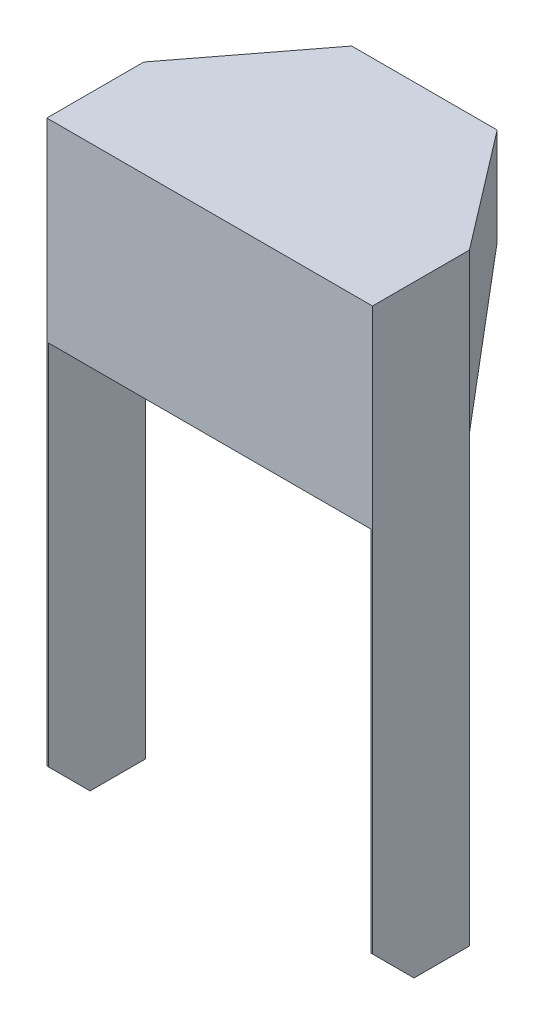
SolidWorks part; units mm, degrees
ref_plane "Front Plane" through (0, 0, 0) normal (0, 0, 1) x (1, 0, 0)
ref_plane "Top Plane" through (0, 0, 0) normal (0, 1, 0) x (1, 0, 0)
ref_plane "Right Plane" through (0, 0, 0) normal (1, 0, 0) x (0, 0, -1)
sketch "Sketch1" plane through (0, 0, 0) normal (0, 1, 0) x (1, 0, 0)
  line L0 (0, 0) -> (0, 155)
  line L1 (0, 155) -> (-52.5, 155)
  line L2 (-52.5, 155) -> (-117.5, 70)
  line L3 (-117.5, 70) -> (-117.5, 0)
  line L4 (-117.5, 0) -> (0, 0)
  dimension "D1" = 117.5
  dimension "D2" = 70
  dimension "D3" = 85
  dimension "D4" = 52.5
extrude "Boss-Extrude1" add sketch "Sketch1" along normal blind 1.2
sketch "Sketch2" plane through (-117.5, 0, 0) normal (-1, 0, 0) x (0, 0, 1)
  line L0 (0, 1.2) -> (0, 0) construction
  line L1 (-70, 1.2) -> (0, 1.2)
  line L2 (-70, 1.2) -> (-70, -433.8)
  line L3 (-70, -433.8) -> (0, -433.8)
  line L4 (0, 1.2) -> (0, -433.8)
  point P5 (0, 1.2)
  dimension "D1" = 435
extrude "Boss-Extrude2" add sketch "Sketch2" against normal blind 1.2
sketch "Sketch3" plane through (-107.9203, 0, -82.5273) normal (-0.7944, 0, -0.6075) x (-0.6075, 0, 0.7944)
  line L0 (15.7703, 0) -> (15.7703, -433.8) construction
  line L1 (-91.2343, 1.2) -> (15.7703, 1.2)
  line L2 (-91.2343, 1.2) -> (-91.2343, -68.8)
  line L3 (-91.2343, -68.8) -> (15.7703, -113.1228)
  line L4 (15.7703, 1.2) -> (15.7703, -113.1228)
  line L5 (-91.2343, -68.8) -> (15.7703, -68.8) construction
  dimension "D1" = 70
  dimension "D2" = 22.5
extrude "Boss-Extrude3" add sketch "Sketch3" against normal blind 1.2
sketch "Sketch4" plane through (0, 0, -155) normal (0, 0, -1) x (-1, 0, 0)
  line L1 (0, 1.2) -> (52.5, 1.2)
  line L2 (0, 1.2) -> (0, -68.8)
  line L3 (0, -68.8) -> (52.5, -68.8)
  line L4 (52.5, 1.2) -> (52.5, -68.8)
extrude "Boss-Extrude4" add sketch "Sketch4" against normal blind 1.2
chamfer "Chamfer1" distance 30 angle 45 1 edges at (-116.9, -433.8, 0)
sketch "Sketch6" plane through (0, 0, 0) normal (0, 0, 1) x (1, 0, 0)
  line L1 (-117.5, 1.2) -> (0, 1.2)
  line L2 (-117.5, 1.2) -> (-117.5, -138.8)
  line L3 (-117.5, -138.8) -> (0, -138.8)
  line L4 (0, 1.2) -> (0, -138.8)
  dimension "D1" = 140
extrude "Boss-Extrude5" add sketch "Sketch6" against normal blind 1.2
mirror "Mirror1"
